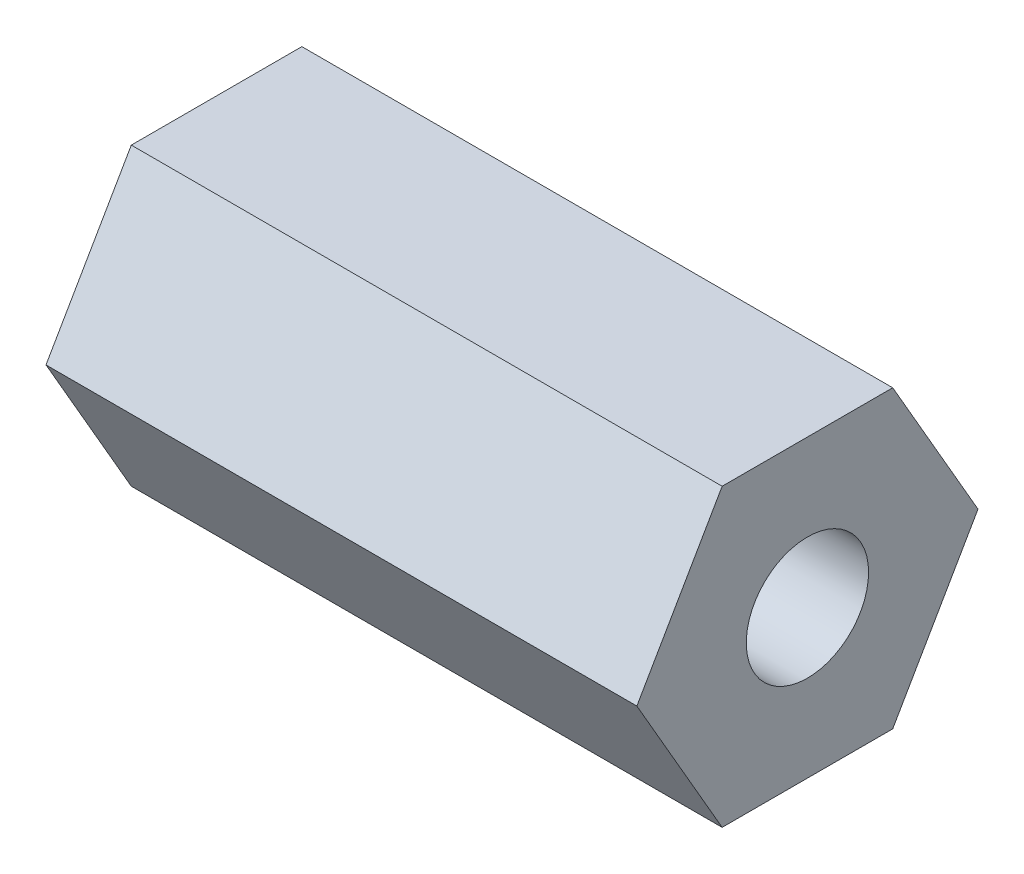
SolidWorks part; units mm, degrees
material "6061-T6 (SS)"
ref_plane "Front Plane" through (0, 0, 0) normal (0, 0, 1) x (1, 0, 0)
ref_plane "Top Plane" through (0, 0, 0) normal (0, 1, 0) x (1, 0, 0)
ref_plane "Right Plane" through (0, 0, 0) normal (1, 0, 0) x (0, 0, -1)
sketch "Sketch1" plane through (0, 0, 0) normal (1, 0, 0) x (0, 0, -1)
  line L1 (3.6662, -6.35) -> (7.3323, 0)
  line L2 (7.3323, 0) -> (3.6662, 6.35)
  line L3 (3.6662, 6.35) -> (-3.6662, 6.35)
  line L4 (-3.6662, 6.35) -> (-7.3323, 0)
  line L5 (-7.3323, 0) -> (-3.6662, -6.35)
  line L6 (-3.6662, -6.35) -> (3.6662, -6.35)
  circle A0 centre (0, 0) radius 6.35 construction
  circle A1 centre (0, 0) radius 2.6289
  dimension "D1" = 5.2578
  dimension "D2" = 12.7
extrude "Boss-Extrude1" add sketch "Sketch1" along normal blind 25.4
